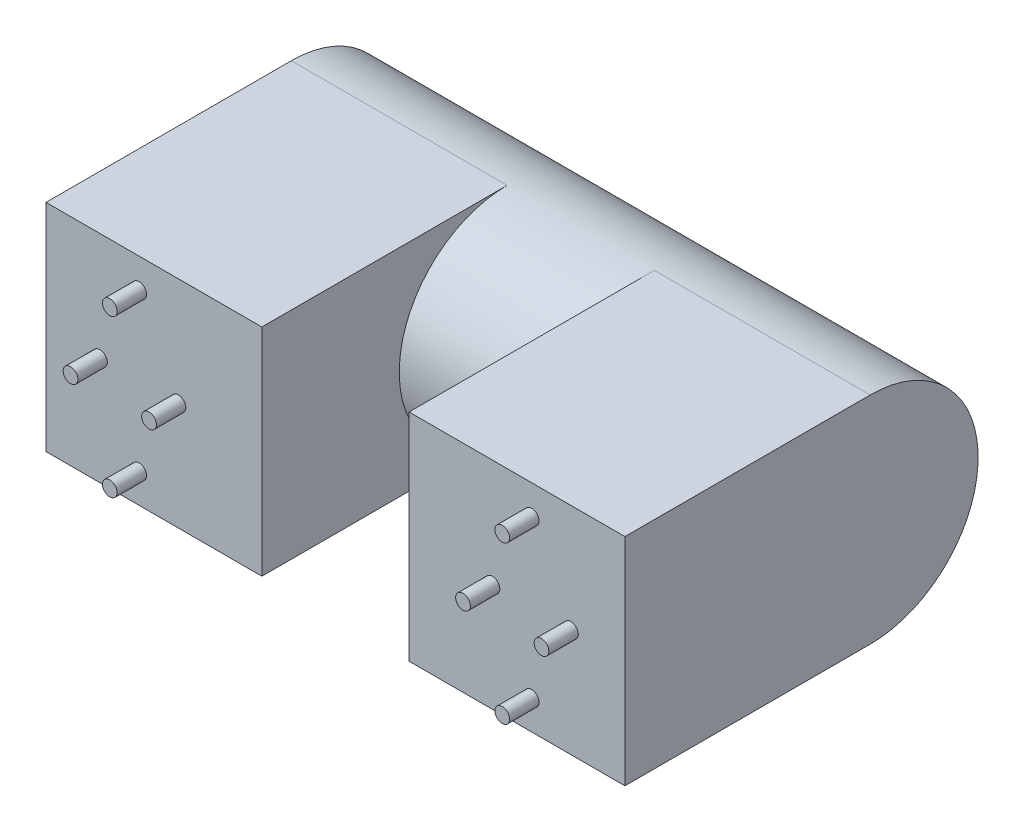
SolidWorks part; units mm, degrees
ref_plane "Plano frontal" through (0, 0, 0) normal (0, 0, 1) x (1, 0, 0)
ref_plane "Plano superior" through (0, 0, 0) normal (0, 1, 0) x (1, 0, 0)
ref_plane "Plano direito" through (0, 0, 0) normal (1, 0, 0) x (0, 0, -1)
sketch "Esboço1" plane through (0, 0, 0) normal (0, 0, 1) x (1, 0, 0)
  line L1 (-11, 11) -> (11, 11)
  line L2 (-11, 11) -> (-11, -11)
  line L3 (-11, -11) -> (11, -11)
  line L4 (11, 11) -> (11, -11)
  line L5 (-11, 11) -> (11, -11) construction
  line L6 (-11, -11) -> (11, 11) construction
  line L7 (48, -11) -> (26, -11)
  line L8 (48, -11) -> (48, 11)
  line L9 (48, 11) -> (26, 11)
  line L10 (26, -11) -> (26, 11)
  line L11 (48, -11) -> (26, 11) construction
  line L12 (48, 11) -> (26, -11) construction
  point P0 (0, 0)
  point P6 (37, 0)
  dimension "D1" = 22
  dimension "D2" = 15
extrude "Ressalto-extrusão1" add sketch "Esboço1" along normal mid plane 48.5
sketch "Esboço2" plane through (11, 0, 0) normal (1, 0, 0) x (0, 0, -1)
  line L2 (-24.25, -11) -> (-24.25, 11) construction
  line L3 (0, 0) -> (0.75, 0) construction
  circle A0 centre (0.75, 0) radius 11
  dimension "D2" = 22
  dimension "D1" = 25
extrude "Ressalto-extrusão2" add sketch "Esboço2" along normal up to surface (15 mm away) up to face at (26, 0, 0)
sketch "Esboço3" plane through (48, 0, 0) normal (1, 0, 0) x (0, 0, -1)
  line L0 (0.75, 11) -> (24.25, 11)
  line L1 (24.25, 11) -> (24.25, -11)
  line L2 (24.25, -11) -> (0.75, -11)
  circle A1 centre (0.75, 0) radius 11
  arc A2 (0.75, -11) -> (0.75, 11) centre (0.75, 0) ccw
  dimension "D1" = 0
extrude "Corte-extrusão1" cut sketch "Esboço3" against normal through all both and the other way through all
sketch "Esboço4" plane through (0, 0, 24.25) normal (0, 0, 1) x (1, 0, 0)
  line L0 (-9.5, 8.75) -> (-9.5, 11) construction
  line L2 (-9.5, -8.75) -> (-9.5, -11) construction
  line L3 (-11, -11) -> (11, -11) construction
  line L4 (-10.25, 8) -> (-11, 8) construction
  line L5 (-11, 11) -> (-11, -11) construction
  line L6 (47.25, 8) -> (48, 8) construction
  line L7 (48, -11) -> (48, 11) construction
  line L8 (11, 11) -> (-11, 11) construction
  line L9 (-9.5, 8) -> (-9.5, 4) construction
  circle A0 centre (-9.5, 8) radius 0.75
  circle A1 centre (-5.5, 8) radius 0.75
  circle A2 centre (-1.5, 8) radius 0.75
  circle A3 centre (2.5, 8) radius 0.75
  circle A4 centre (6.5, 8) radius 0.75
  circle A10 centre (30.5, 8) radius 0.75
  circle A11 centre (34.5, 8) radius 0.75
  circle A12 centre (38.5, 8) radius 0.75
  circle A13 centre (42.5, 8) radius 0.75
  circle A14 centre (46.5, 8) radius 0.75
  circle A16 centre (-5.5, 4) radius 0.75
  circle A17 centre (-1.5, 4) radius 0.75
  circle A18 centre (2.5, 4) radius 0.75
  circle A19 centre (6.5, 4) radius 0.75
  circle A25 centre (30.5, 4) radius 0.75
  circle A26 centre (34.5, 4) radius 0.75
  circle A27 centre (38.5, 4) radius 0.75
  circle A28 centre (42.5, 4) radius 0.75
  circle A29 centre (46.5, 4) radius 0.75
  circle A31 centre (-5.5, 0) radius 0.75
  circle A32 centre (-1.5, 0) radius 0.75
  circle A33 centre (2.5, 0) radius 0.75
  circle A34 centre (6.5, 0) radius 0.75
  circle A40 centre (30.5, 0) radius 0.75
  circle A41 centre (34.5, 0) radius 0.75
  circle A42 centre (38.5, 0) radius 0.75
  circle A43 centre (42.5, 0) radius 0.75
  circle A44 centre (46.5, 0) radius 0.75
  circle A46 centre (-5.5, -4) radius 0.75
  circle A47 centre (-1.5, -4) radius 0.75
  circle A48 centre (2.5, -4) radius 0.75
  circle A49 centre (6.5, -4) radius 0.75
  circle A55 centre (30.5, -4) radius 0.75
  circle A56 centre (34.5, -4) radius 0.75
  circle A57 centre (38.5, -4) radius 0.75
  circle A58 centre (42.5, -4) radius 0.75
  circle A59 centre (46.5, -4) radius 0.75
  circle A61 centre (-5.5, -8) radius 0.75
  circle A62 centre (-1.5, -8) radius 0.75
  circle A63 centre (2.5, -8) radius 0.75
  circle A64 centre (6.5, -8) radius 0.75
  circle A70 centre (30.5, -8) radius 0.75
  circle A71 centre (34.5, -8) radius 0.75
  circle A72 centre (38.5, -8) radius 0.75
  circle A73 centre (42.5, -8) radius 0.75
  circle A74 centre (46.5, -8) radius 0.75
  circle A106 centre (-9.5, 4) radius 0.75
  circle A107 centre (-9.5, 0) radius 0.75
  circle A108 centre (-9.5, -4) radius 0.75
  circle A109 centre (-9.5, -8) radius 0.75
  circle A110 centre (10.5, 8) radius 0.75 [skipped]
  circle A111 centre (14.5, 8) radius 0.75 [skipped]
  circle A112 centre (18.5, 8) radius 0.75 [skipped]
  circle A113 centre (22.5, 8) radius 0.75 [skipped]
  circle A114 centre (26.5, 8) radius 0.75 [skipped]
  circle A115 centre (10.5, 4) radius 0.75 [skipped]
  circle A116 centre (14.5, 4) radius 0.75 [skipped]
  circle A117 centre (18.5, 4) radius 0.75 [skipped]
  circle A118 centre (22.5, 4) radius 0.75 [skipped]
  circle A119 centre (26.5, 4) radius 0.75 [skipped]
  circle A120 centre (10.5, 0) radius 0.75 [skipped]
  circle A121 centre (14.5, 0) radius 0.75 [skipped]
  circle A122 centre (18.5, 0) radius 0.75 [skipped]
  circle A123 centre (22.5, 0) radius 0.75 [skipped]
  circle A124 centre (26.5, 0) radius 0.75 [skipped]
  circle A125 centre (10.5, -4) radius 0.75 [skipped]
  circle A126 centre (14.5, -4) radius 0.75 [skipped]
  circle A127 centre (18.5, -4) radius 0.75 [skipped]
  circle A128 centre (22.5, -4) radius 0.75 [skipped]
  circle A129 centre (26.5, -4) radius 0.75 [skipped]
  circle A130 centre (10.5, -8) radius 0.75 [skipped]
  circle A131 centre (14.5, -8) radius 0.75 [skipped]
  circle A132 centre (18.5, -8) radius 0.75 [skipped]
  circle A133 centre (22.5, -8) radius 0.75 [skipped]
  circle A134 centre (26.5, -8) radius 0.75 [skipped]
  point P20 (0, 0)
  dimension "D1" = 15
  dimension "D5" = 1.5
  dimension "D2" = 5
  dimension "D3" = 4
  dimension "D4" = 4
extrude "Ressalto-extrusão3" add sketch "Esboço4" along normal blind 3 contours A31 | A33 | A2 | A62 | A41 | A43 | A72 | A12
